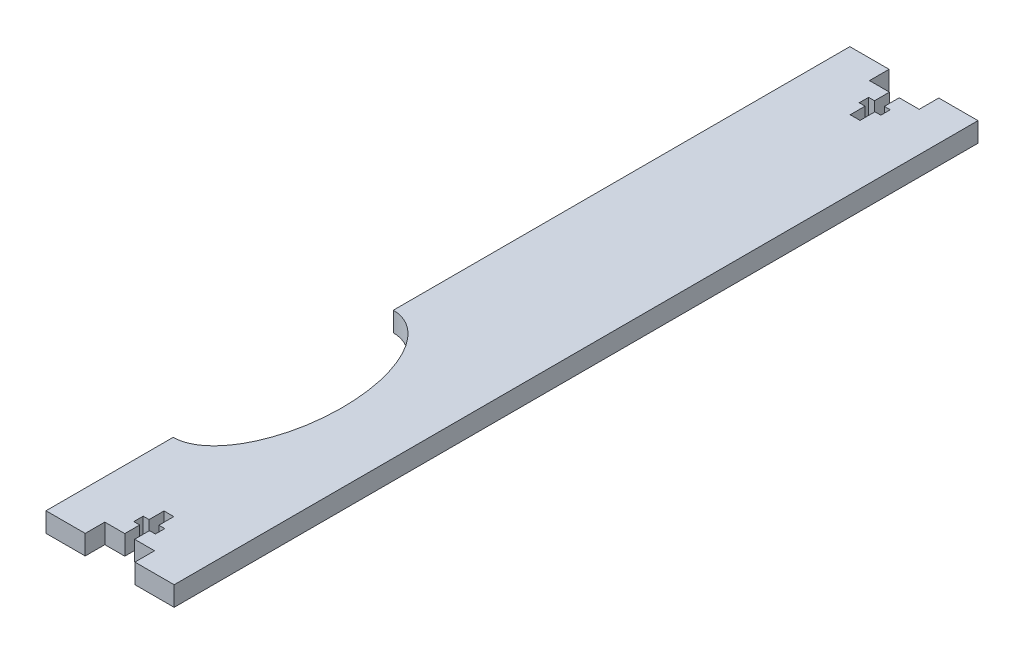
SolidWorks part; units mm, degrees
material "PMMA"
ref_plane "Front Plane" through (0, 0, 0) normal (0, 0, 1) x (1, 0, 0)
ref_plane "Top Plane" through (0, 0, 0) normal (0, 1, 0) x (1, 0, 0)
ref_plane "Right Plane" through (0, 0, 0) normal (1, 0, 0) x (0, 0, -1)
sketch "Schizzo1" plane through (0, 0, 0) normal (0, 1, 0) x (1, 0, 0)
  line L0 (16.34, 102.5) -> (-16.34, -102.5) construction
  line L1 (-16.34, 102.5) -> (16.34, 102.5)
  line L2 (-16.34, 102.5) -> (-16.34, -102.5)
  line L3 (-16.34, -102.5) -> (16.34, -102.5)
  line L4 (16.34, 102.5) -> (16.34, -102.5)
  point P4 (0, 0)
  dimension "D1" = 205
  dimension "D2" = 32.68
extrude "Estrusione-Estrusione1" add sketch "Schizzo1" along normal blind 5
sketch "Schizzo3" plane through (0, 0, 0) normal (0, 1, 0) x (1, 0, 0)
  line L0 (16.34, 102.5) -> (-16.34, 102.5) construction
  line L1 (-6.34, 102.5) -> (6.34, 102.5)
  line L2 (-6.34, 102.5) -> (-6.34, 97.5)
  line L3 (-6.34, 97.5) -> (6.34, 97.5)
  line L4 (6.34, 102.5) -> (6.34, 97.5)
  line L5 (-16.34, 102.5) -> (-16.34, -102.5) construction
  line L6 (-16.34, 0) -> (16.34, 0) construction
  line L7 (16.34, -102.5) -> (16.34, 102.5) construction
  line L8 (-6.34, -102.5) -> (-6.34, -97.5)
  line L9 (-6.34, -102.5) -> (6.34, -102.5)
  line L10 (6.34, -102.5) -> (6.34, -97.5)
  line L11 (-6.34, -97.5) -> (6.34, -97.5)
  dimension "D1" = 5
  dimension "D2" = 12.68
  dimension "D3" = 10
extrude "Taglio-Estrusione1" cut sketch "Schizzo3" along direction (0, 1, 0) on the side of the normal through all
sketch "Schizzo4" plane through (0, 0, 0) normal (0, 1, 0) x (1, 0, 0)
  line L0 (0, 168.8652) -> (0, 26.1348) construction
  line L1 (0, 87.5) -> (0, 97.5) construction
  line L2 (-1.25, 87.5) -> (-1.25, 91.3)
  line L3 (-1.25, 91.3) -> (-2.75, 91.3)
  line L4 (-2.75, 91.3) -> (-2.75, 93.7)
  line L5 (-2.75, 93.7) -> (-1.25, 93.7)
  line L6 (-1.25, 93.7) -> (-1.25, 97.5)
  line L7 (-1.25, 97.5) -> (1.25, 97.5)
  line L8 (1.25, 97.5) -> (1.25, 93.7)
  line L9 (1.25, 93.7) -> (2.75, 93.7)
  line L10 (2.75, 93.7) -> (2.75, 91.3)
  line L11 (2.75, 91.3) -> (1.25, 91.3)
  line L12 (1.25, 91.3) -> (1.25, 87.5)
  line L13 (1.25, 87.5) -> (-1.25, 87.5)
  line L14 (0, 97.5) -> (0, -97.5) construction
  line L15 (-6.34, 97.5) -> (6.34, 97.5) construction
  line L16 (6.34, -97.5) -> (-6.34, -97.5) construction
  line L17 (16.34, 0) -> (-16.34, 0) construction
  line L18 (16.34, -102.5) -> (16.34, 102.5) construction
  line L19 (-16.34, 102.5) -> (-16.34, -102.5) construction
  line L20 (2.75, -91.3) -> (1.25, -91.3)
  line L21 (2.75, -93.7) -> (2.75, -91.3)
  line L22 (1.25, -93.7) -> (2.75, -93.7)
  line L23 (1.25, -97.5) -> (1.25, -93.7)
  line L24 (-1.25, -97.5) -> (1.25, -97.5)
  line L25 (-1.25, -93.7) -> (-1.25, -97.5)
  line L26 (-2.75, -93.7) -> (-1.25, -93.7)
  line L27 (-2.75, -91.3) -> (-2.75, -93.7)
  line L28 (-1.25, -91.3) -> (-2.75, -91.3)
  line L29 (-1.25, -87.5) -> (-1.25, -91.3)
  line L30 (1.25, -87.5) -> (-1.25, -87.5)
  line L31 (1.25, -91.3) -> (1.25, -87.5)
  dimension "D1" = 5.5
  dimension "D2" = 2.5
  dimension "D3" = 1.25
  dimension "D4" = 2.75
  dimension "D5" = 2.4
  dimension "D6" = 10
  dimension "D7" = 90
  dimension "D8" = 90
extrude "Taglio-Estrusione2" cut sketch "Schizzo4" along direction (0, 1, 0) on the side of the normal through all
sketch "Schizzo5" plane through (0, 0, 0) normal (0, 1, 0) x (1, 0, 0)
  line L0 (-16.34, 102.5) -> (-16.34, -102.5) construction
  line L3 (-16.34, -102.5) -> (-6.34, -102.5) construction
  ellipse E1 centre (-16.34, -42) end of major axis (-16.34, -13.9281) minor radius 15
  dimension "D3" = 60.5
  dimension "D4" = 15
extrude "Taglio-Estrusione3" cut sketch "Schizzo5" along direction (0, 1, 0) on the side of the normal through all
equation "\"Thickness5\"=5"
equation "\"D1@Estrusione-Estrusione1\"=\"Thickness5\""
equation "\"D1@Schizzo3\"=\"Thickness5\""
